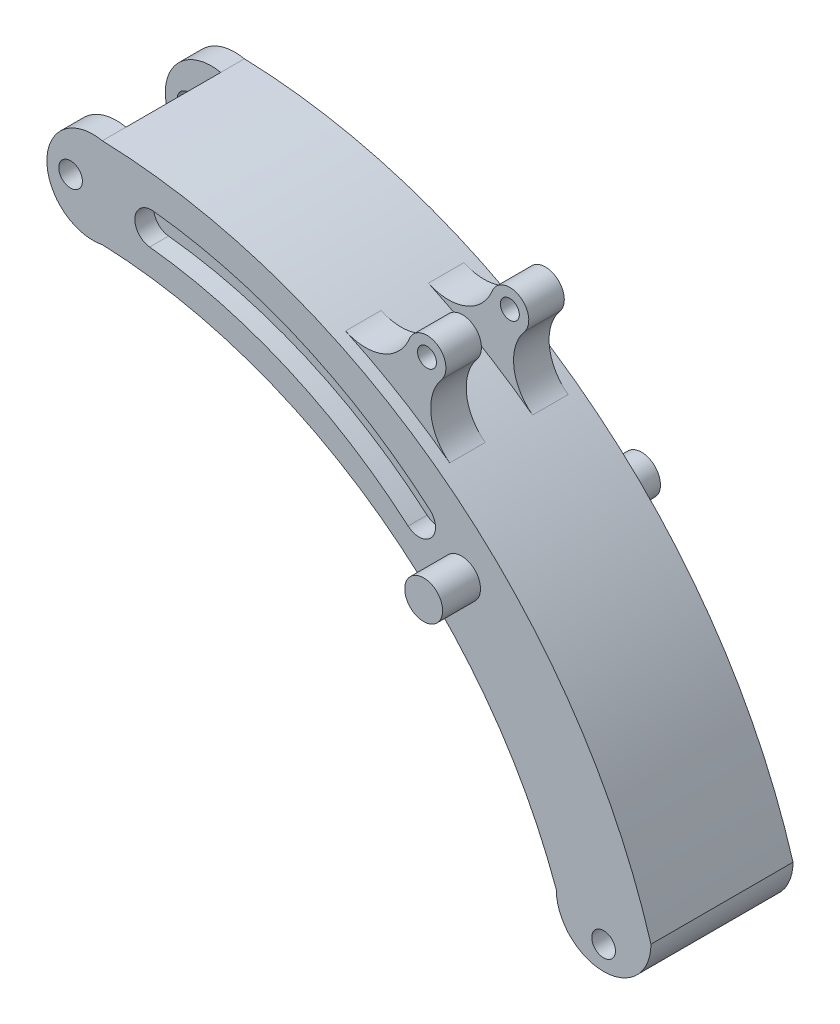
SolidWorks part; units mm, degrees
ref_plane "Ön Düzlem" through (0, 0, 0) normal (0, 0, 1) x (1, 0, 0)
ref_plane "Üst Düzlem" through (0, 0, 0) normal (0, 1, 0) x (1, 0, 0)
ref_plane "Sağ Düzlem" through (0, 0, 0) normal (1, 0, 0) x (0, 0, -1)
sketch "Çizim1" plane through (0, 0, 0) normal (0, 0, 1) x (1, 0, 0)
  line L0 (0, 0) -> (-76.496, 0) construction
  line L1 (0, 0) -> (52.8081, 0) construction
  line L2 (-95.8579, 89.0107) -> (-95.8579, 70)
  line L3 (0, 0) -> (20, 0)
  arc A0 (0, 0) -> (-95.8579, 70) centre (-99.725, -35.9294) ccw
  arc A1 (20, 0) -> (-95.8579, 89.0107) centre (-99.725, -35.9294) ccw
  dimension "D1" = 20
  dimension "D2" = 106
  dimension "D3" = 125
  dimension "D4" = 70
extrude "Yükseklik-Ekstrüzyon1" add sketch "Çizim1" along normal mid plane 30
sketch "Çizim2" plane through (-95.8579, 0, 0) normal (-1, 0, 0) x (0, 0, 1)
  line L0 (15, 70) -> (-15, 70) construction
  line L1 (-15, 89.0107) -> (-15, 70) construction
  line L2 (15, 89.0107) -> (-15, 89.0107) construction
  line L3 (15, 89.0107) -> (15, 70) construction
  line L4 (15, 70) -> (-15, 70)
  line L5 (-15, 89.0107) -> (-15, 70)
  line L6 (15, 89.0107) -> (-15, 89.0107)
  line L7 (15, 89.0107) -> (15, 70)
sketch "Çizim3" plane through (0, 0, 15) normal (0, 0, 1) x (1, 0, 0)
  line L0 (-95.8579, 89.0107) -> (-95.8579, 70)
  arc A0 (-95.8579, 89.0107) -> (-95.8579, 70) centre (-97.8579, 79.5054) ccw
  dimension "D1" = 2
extrude "Yükseklik-Ekstrüzyon2" add sketch "Çizim3" against normal blind 5
mirror "Aynalama1" about plane through (0, 0, 0) normal (0, 0, 1) of "Yükseklik-Ekstrüzyon2"
sketch "Çizim4" plane through (0, 0, 15) normal (0, 0, 1) x (1, 0, 0)
  line L0 (-97.8579, 79.5054) -> (-107.5714, 79.5054) construction
  arc A1 (-95.8579, 89.0107) -> (-95.8579, 70) centre (-97.8579, 79.5054) ccw construction
  circle A2 centre (-102.5714, 79.5054) radius 2.5
  dimension "D1" = 5
  dimension "D2" = 5
extrude "Kes-Ekstrüzyon1" cut sketch "Çizim4" against normal through all
sketch "Çizim5" plane through (0, 0, 0) normal (0, 0, 1) x (1, 0, 0)
  arc A0 (20, 0) -> (-95.8579, 89.0107) centre (-99.725, -35.9294) ccw construction
  arc A1 (-25, 64.2762) -> (-47, 77.4067) centre (-99.725, -35.9294) ccw
  arc A2 (-47, 77.4067) -> (-33.5119, 82.7232) centre (-42.782, 86.4736) ccw
  arc A3 (-26.7233, 78.6715) -> (-33.5119, 82.7232) centre (-29.8039, 81.223) ccw
  arc A4 (-25, 64.2762) -> (-26.7233, 78.6715) centre (-19.022, 72.2927) cw
  dimension "D1" = 8
  dimension "D2" = 10
  dimension "D3" = 10
  dimension "D4" = 25
  dimension "D5" = 22
extrude "Yükseklik-Ekstrüzyon3" add sketch "Çizim5" along normal mid plane 25
sketch "Çizim6" plane through (0, 0, 0) normal (0, 0, 1) x (1, 0, 0)
  arc A0 (-25, 64.2762) -> (-47, 77.4067) centre (-99.725, -35.9294) ccw construction
  arc A1 (-26.7233, 78.6715) -> (-25, 64.2762) centre (-19.022, 72.2927) ccw construction
  arc A2 (-26.7233, 78.6715) -> (-33.5119, 82.7232) centre (-29.8039, 81.223) ccw construction
  arc A3 (-47, 77.4067) -> (-33.5119, 82.7232) centre (-42.782, 86.4736) ccw construction
  arc A4 (-25, 64.2762) -> (-47, 77.4067) centre (-99.725, -35.9294) ccw
  arc A5 (-26.7233, 78.6715) -> (-25, 64.2762) centre (-19.022, 72.2927) ccw
  arc A6 (-26.7233, 78.6715) -> (-33.5119, 82.7232) centre (-29.8039, 81.223) ccw
  arc A7 (-47, 77.4067) -> (-33.5119, 82.7232) centre (-42.782, 86.4736) ccw
extrude "Kes-Ekstrüzyon2" cut sketch "Çizim6" against normal mid plane 10
sketch "Çizim7" plane through (0, 0, 12.5) normal (0, 0, 1) x (1, 0, 0)
  circle A0 centre (-29.8039, 81.223) radius 2
  dimension "D1" = 4
extrude "Kes-Ekstrüzyon3" cut sketch "Çizim7" against normal through all
sketch "Çizim8" plane through (0, 0, 15) normal (0, 0, 1) x (1, 0, 0)
  circle A0 centre (-20, 47) radius 4
  dimension "D1" = 20
  dimension "D3" = 8
  dimension "D2" = 47
extrude "Yükseklik-Ekstrüzyon5" add sketch "Çizim8" along normal blind 8
mirror "Aynalama2" about plane through (0, 0, 0) normal (0, 0, 1) of "Yükseklik-Ekstrüzyon5"
sketch "Çizim9" plane through (0, 0, 15) normal (0, 0, 1) x (1, 0, 0)
  arc A0 (-85.5, 78.0583) -> (-29, 53.4796) centre (-96.6682, -24.8431) cw construction
  arc A1 (-26.7118, 56.128) -> (-85.1224, 81.5379) centre (-96.6682, -24.8431) ccw
  arc A2 (-31.2882, 50.8311) -> (-85.8776, 74.5787) centre (-96.6682, -24.8431) ccw
  arc A3 (-31.2882, 50.8311) -> (-26.7118, 56.128) centre (-29, 53.4796) ccw
  arc A4 (-85.1224, 81.5379) -> (-85.8776, 74.5787) centre (-85.5, 78.0583) ccw
  arc A6 (20, 0) -> (-95.8579, 89.0107) centre (-99.725, -35.9294) ccw construction
  arc A7 (0, 0) -> (-95.8579, 70) centre (-99.725, -35.9294) ccw construction
  point P3 (-55.3787, 70.0706)
  dimension "D1" = 29
  dimension "D2" = 3.5
  dimension "D3" = 106
  dimension "D4" = 11.5
  dimension "D5" = 85.5
  dimension "D6" = 114
extrude "Kes-Ekstrüzyon4" cut sketch "Çizim9" against normal blind 4
mirror "Aynalama3" about plane through (0, 0, 0) normal (0, 0, 1) of "Kes-Ekstrüzyon4"
sketch "Çizim10" plane through (0, 0, 0) normal (0, 0, 1) x (1, 0, 0)
  line L0 (0, 0) -> (20, 0)
  arc A0 (0, 0) -> (20, 0) centre (10, 0) ccw
  dimension "D1" = 10
extrude "Yükseklik-Ekstrüzyon6" add sketch "Çizim10" along normal mid plane 30
sketch "Çizim11" plane through (0, 0, 15) normal (0, 0, 1) x (1, 0, 0)
  circle A0 centre (10, -5) radius 2.5
  arc A1 (0, 0) -> (20, 0) centre (10, 0) ccw construction
  dimension "D1" = 5
  dimension "D2" = 10
  dimension "D3" = 5
extrude "Kes-Ekstrüzyon5" cut sketch "Çizim11" against normal blind 30
